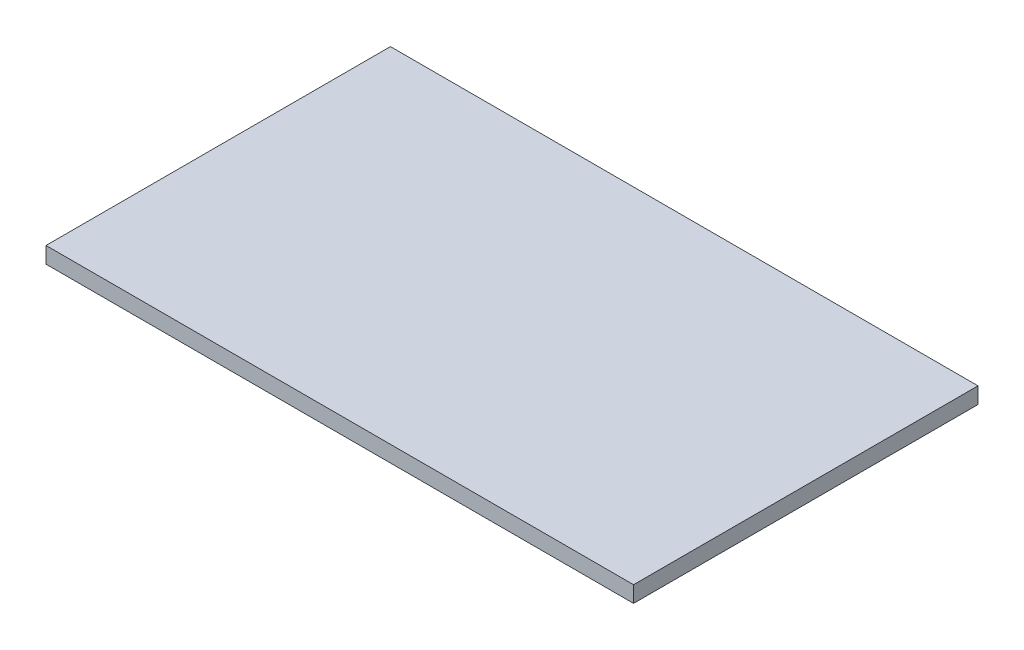
SolidWorks part; units mm, degrees
material "6061 Alloy"
ref_plane "Front Plane" through (0, 0, 0) normal (0, 0, 1) x (1, 0, 0)
ref_plane "Top Plane" through (0, 0, 0) normal (0, 1, 0) x (1, 0, 0)
ref_plane "Right Plane" through (0, 0, 0) normal (1, 0, 0) x (0, 0, -1)
sketch "Sketch1" plane through (0, 0, 0) normal (0, 1, 0) x (1, 0, 0)
  line L1 (-72.5, -42.5) -> (72.5, -42.5)
  line L2 (-72.5, -42.5) -> (-72.5, 42.5)
  line L3 (-72.5, 42.5) -> (72.5, 42.5)
  line L4 (72.5, -42.5) -> (72.5, 42.5)
  line L5 (-72.5, -42.5) -> (72.5, 42.5) construction
  line L6 (-72.5, 42.5) -> (72.5, -42.5) construction
  point P0 (0, 0)
  dimension "D1" = 145
  dimension "D2" = 85
extrude "Boss-Extrude1" add sketch "Sketch1" along normal blind 4
